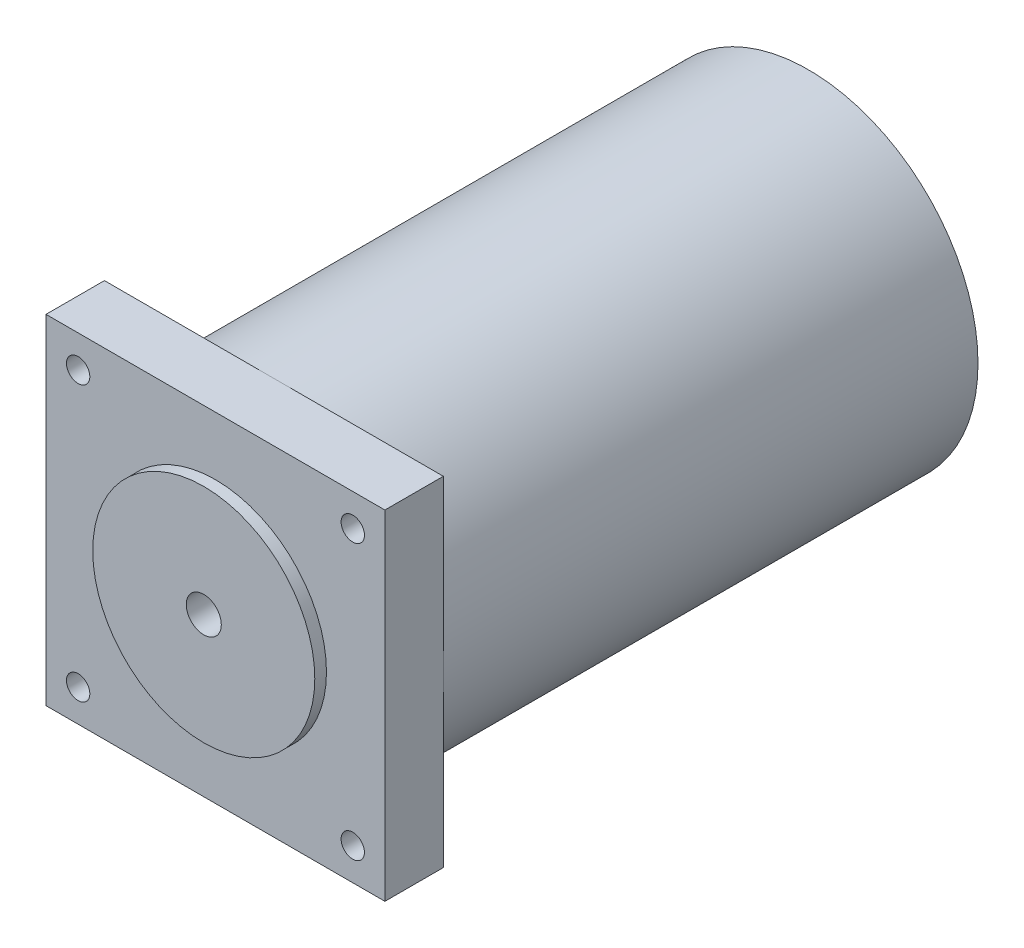
SolidWorks part; units mm, degrees
material "1060 Alloy"
ref_plane "Front Plane" through (0, 0, 0) normal (0, 0, 1) x (1, 0, 0)
ref_plane "Top Plane" through (0, 0, 0) normal (0, 1, 0) x (1, 0, 0)
ref_plane "Right Plane" through (0, 0, 0) normal (1, 0, 0) x (0, 0, -1)
sketch "Sketch1" plane through (0, 0, 0) normal (0, 0, 1) x (1, 0, 0)
  circle A0 centre (0, 0) radius 19
  dimension "D1" = 38
extrude "Boss-Extrude1" add sketch "Sketch1" against normal blind 2
sketch "Sketch3" plane through (0, 0, -2) normal (0, 0, -1) x (-1, 0, 0)
  line L0 (0, 0) -> (-29, 0) construction
  line L1 (-29, 0) -> (-29, 29) construction
  line L3 (-29, 29) -> (29, 29)
  line L4 (-29, 29) -> (-29, -29)
  line L5 (-29, -29) -> (29, -29)
  line L6 (29, 29) -> (29, -29)
  dimension "D1" = 29
  dimension "D2" = 29
  dimension "D3" = 58
extrude "Boss-Extrude2" add sketch "Sketch3" along normal blind 10
sketch "Sketch4" plane through (0, 0, -12) normal (0, 0, -1) x (-1, 0, 0)
  circle A0 centre (0, 0) radius 29
  dimension "D1" = 58
extrude "Boss-Extrude3" add sketch "Sketch4" along normal blind 91.5
sketch "Sketch5" plane through (0, 0, -2) normal (0, 0, 1) x (1, 0, 0)
  line L0 (-29, 29) -> (-29, 23.5) construction
  line L1 (-29, -29) -> (-29, 29) construction
  line L2 (-29, 23.5) -> (-23.5, 23.5) construction
  line L3 (0, 29) -> (0, -29) construction
  line L4 (-29, 29) -> (29, 29) construction
  line L5 (29, -29) -> (-29, -29) construction
  line L6 (-29, 0) -> (29, 0) construction
  circle A0 centre (-23.5, 23.5) radius 2
  circle A1 centre (23.5, 23.5) radius 2
  circle A2 centre (23.5, -23.5) radius 2
  circle A3 centre (-23.5, -23.5) radius 2
  dimension "D3" = 4
  dimension "D1" = 5.5
  dimension "D2" = 5.5
extrude "Cut-Extrude1" cut sketch "Sketch5" against normal blind 10
sketch "Sketch6" plane through (0, 0, 0) normal (0, 0, 1) x (1, 0, 0)
  circle A0 centre (0, 0) radius 3
  dimension "D1" = 6
extrude "Cut-Extrude2" cut sketch "Sketch6" against normal blind 12
